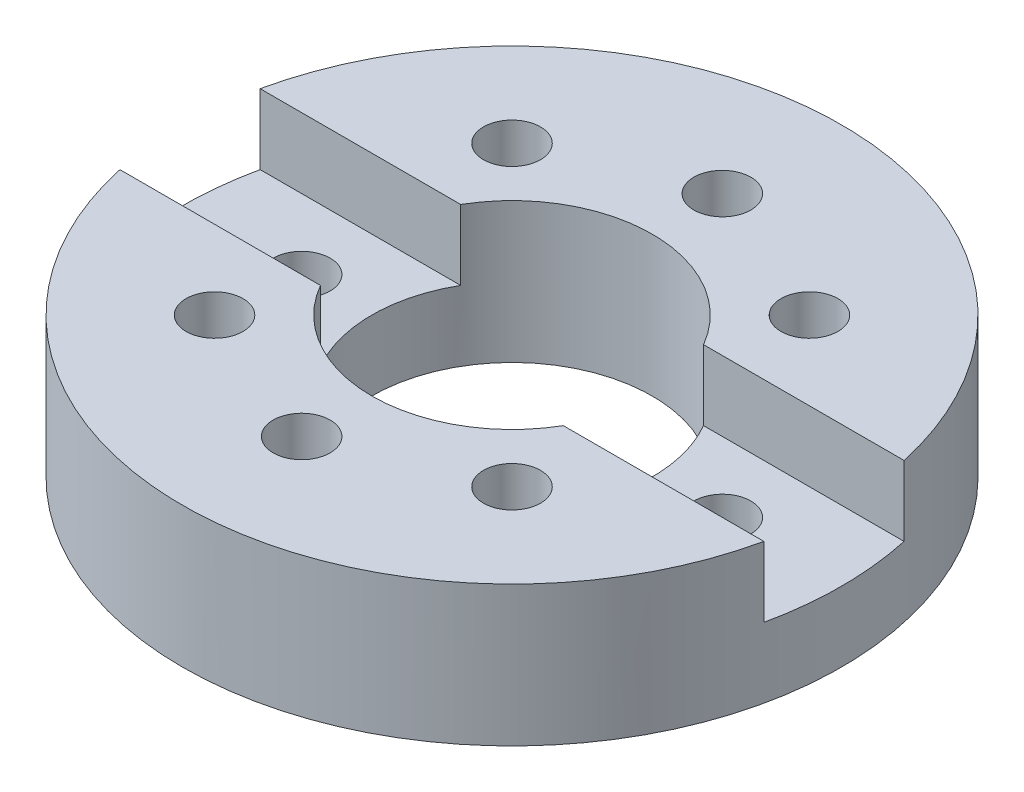
SolidWorks part; units mm, degrees
material "Ceramic Porcelain"
ref_plane "Front Plane" through (0, 0, 0) normal (0, 0, 1) x (1, 0, 0)
ref_plane "Top Plane" through (0, 0, 0) normal (0, 1, 0) x (1, 0, 0)
ref_plane "Right Plane" through (0, 0, 0) normal (1, 0, 0) x (0, 0, -1)
sketch "Sketch1" plane through (0, 0, 0) normal (0, 1, 0) x (1, 0, 0)
  circle A0 centre (0, 0) radius 2.35
  circle A1 centre (0, 1.5) radius 0.2032
  circle A2 centre (1.0607, 1.0607) radius 0.2032
  circle A3 centre (1.5, 0) radius 0.2032
  circle A4 centre (1.0607, -1.0607) radius 0.2032
  circle A5 centre (0, -1.5) radius 0.2032
  circle A6 centre (-1.0607, -1.0607) radius 0.2032
  circle A7 centre (-1.5, 0) radius 0.2032
  circle A8 centre (-1.0607, 1.0607) radius 0.2032
  point P21 (0, 0)
  point P22 (0, 0)
  dimension "D1" = 1.5
  dimension "D3" = 0.4064
  dimension "D4" = 4.7
  dimension "D2" = 8
extrude "Boss-Extrude1" add sketch "Sketch1" along normal blind 1
sketch "Sketch2" plane through (0, 1, 0) normal (0, 1, 0) x (1, 0, 0)
  circle A0 centre (0, 0) radius 1 construction
  dimension "D1" = 1
sketch "Sketch3" plane through (0, 1, 0) normal (0, 1, 0) x (1, 0, 0)
  circle A0 centre (0, 0) radius 1
  dimension "D1" = 2
extrude "Cut-Extrude1" cut sketch "Sketch3" against normal through all
sketch "Sketch4" plane through (0, 1, 0) normal (0, 1, 0) x (1, 0, 0)
  line L1 (-2.35, 0.5) -> (2.35, 0.5)
  line L3 (-2.35, -0.5) -> (2.35, -0.5)
  arc A0 (-2.35, -0.5) -> (-2.35, 0.5) centre (-2.35, 0) cw
  circle A1 centre (0, 0) radius 2.35 construction
  circle A2 centre (0, 0) radius 2.35 construction
  arc A3 (2.35, -0.5) -> (2.35, 0.5) centre (2.35, 0) ccw
  dimension "D1" = 1
  dimension "D2" = 0.5
extrude "Cut-Extrude2" cut sketch "Sketch4" against normal offset from surface (0.5 mm away) 0.5 up to face at (0, 0, 1)
